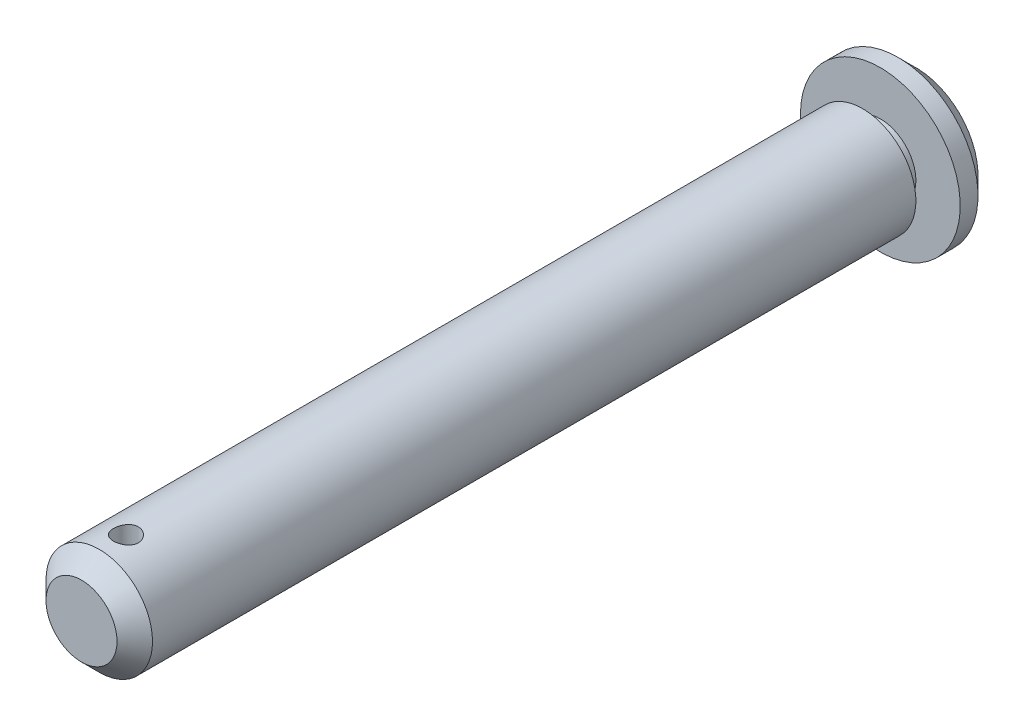
SolidWorks part; units mm, degrees
material "AISI 1045 钢，冷拔"
ref_plane "前视基准面" through (0, 0, 0) normal (0, 0, 1) x (1, 0, 0)
ref_plane "上视基准面" through (0, 0, 0) normal (0, 1, 0) x (1, 0, 0)
ref_plane "右视基准面" through (0, 0, 0) normal (1, 0, 0) x (0, 0, -1)
sketch "草图1" plane through (0, 0, 0) normal (0, 1, 0) x (1, 0, 0)
  line L0 (0, 0) -> (-3, 0)
  line L1 (-3, 0) -> (-3, 44)
  line L2 (-3, 44) -> (-2, 44)
  line L3 (-2, 44) -> (-2, 45)
  line L4 (-2, 45) -> (-4.5, 45)
  line L5 (-4.5, 45) -> (-4.5, 47)
  line L6 (-4.5, 47) -> (0, 47)
  line L7 (0, 47) -> (0, 0)
  dimension "D1" = 2
  dimension "D2" = 47
  dimension "D3" = 1
  dimension "D4" = 1
  dimension "D5" = 4.5
  dimension "D6" = 3
revolve "旋转1" add sketch "草图1" angle 360 about L7
sketch "草图2" plane through (0, 0, 0) normal (0, 1, 0) x (1, 0, 0)
  circle A0 centre (0, 2.5) radius 0.7
  dimension "D1" = 1.4
  dimension "D2" = 2.5
extrude "切除-拉伸1" cut sketch "草图2" against normal through all both and the other way through all
chamfer "倒角1" distance 1 angle 45 2 edges at (-3, 0, 0) (-4.5, 0, -47)
